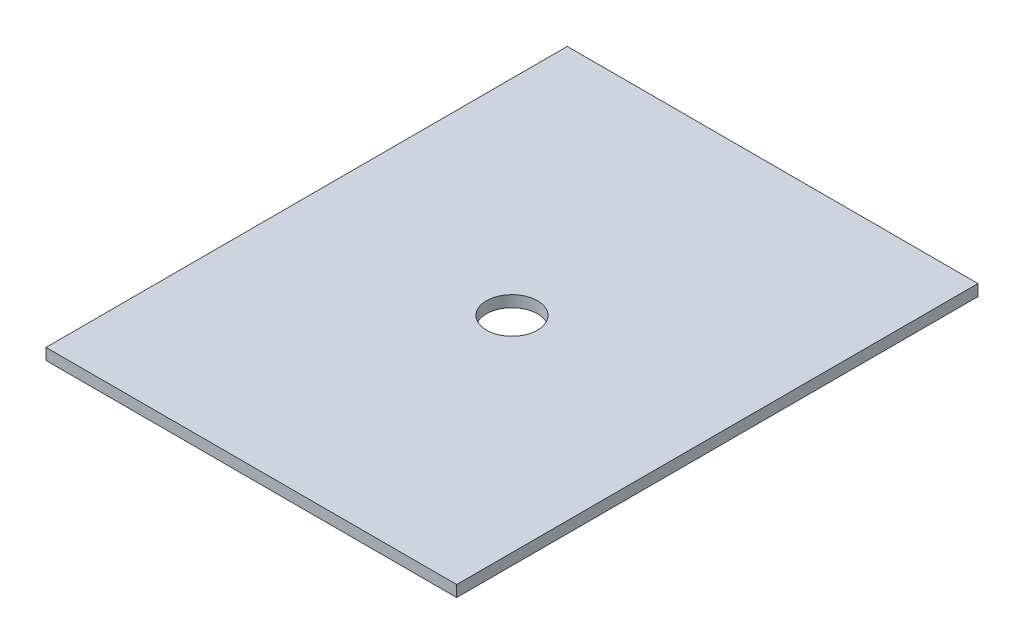
SolidWorks part; units mm, degrees
ref_plane "Front Plane" through (0, 0, 0) normal (0, 0, 1) x (1, 0, 0)
ref_plane "Top Plane" through (0, 0, 0) normal (0, 1, 0) x (1, 0, 0)
ref_plane "Right Plane" through (0, 0, 0) normal (1, 0, 0) x (0, 0, -1)
sketch "Sketch1" plane through (0, 0, 0) normal (0, 1, 0) x (1, 0, 0)
  line L1 (0, 0) -> (230.124, 0)
  line L2 (0, 0) -> (0, 292.1)
  line L3 (0, 292.1) -> (230.124, 292.1)
  line L4 (230.124, 0) -> (230.124, 292.1)
  dimension "D1" = 292.1
  dimension "D2" = 230.124
extrude "Boss-Extrude1" add sketch "Sketch1" along normal blind 6.35
sketch "Sketch2" plane through (0, 6.35, 0) normal (0, 1, 0) x (1, 0, 0)
  line L0 (230.124, 0) -> (230.124, 292.1) construction
  line L1 (230.124, 292.1) -> (0, 292.1) construction
  circle A0 centre (115.062, 146.05) radius 14.2875
  point P4 (230.124, 146.05)
  point P5 (118.896, 146.05)
  point P8 (115.062, 292.1)
  dimension "D1" = 28.575
extrude "Cut-Extrude1" cut sketch "Sketch2" against normal blind 6.35
